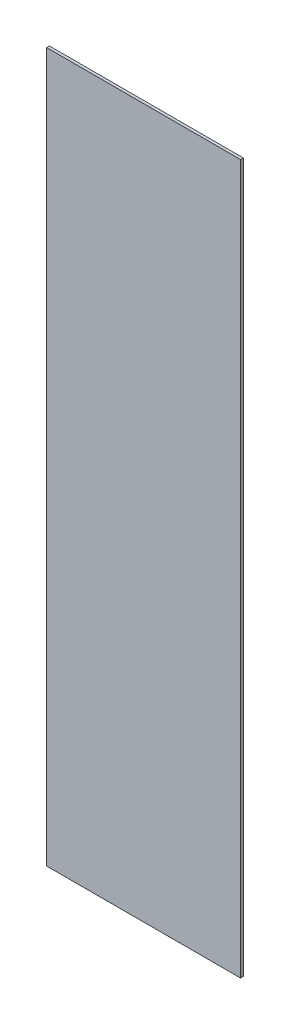
SolidWorks part; units mm, degrees
material "PVC Rigid"
ref_plane "Front Plane" through (0, 0, 0) normal (0, 0, 1) x (1, 0, 0)
ref_plane "Top Plane" through (0, 0, 0) normal (0, 1, 0) x (1, 0, 0)
ref_plane "Right Plane" through (0, 0, 0) normal (1, 0, 0) x (0, 0, -1)
sketch "Sketch1" plane through (0, 0, 0) normal (0, 0, 1) x (1, 0, 0)
  line L1 (-96.3284, 227.584) -> (81.4716, 227.584)
  line L2 (-96.3284, 227.584) -> (-96.3284, -422.656)
  line L3 (-96.3284, -422.656) -> (81.4716, -422.656)
  line L4 (81.4716, 227.584) -> (81.4716, -422.656)
  dimension "D1" = 650.24
  dimension "D2" = 177.8
extrude "Boss-Extrude1" add sketch "Sketch1" along normal blind 2.54
